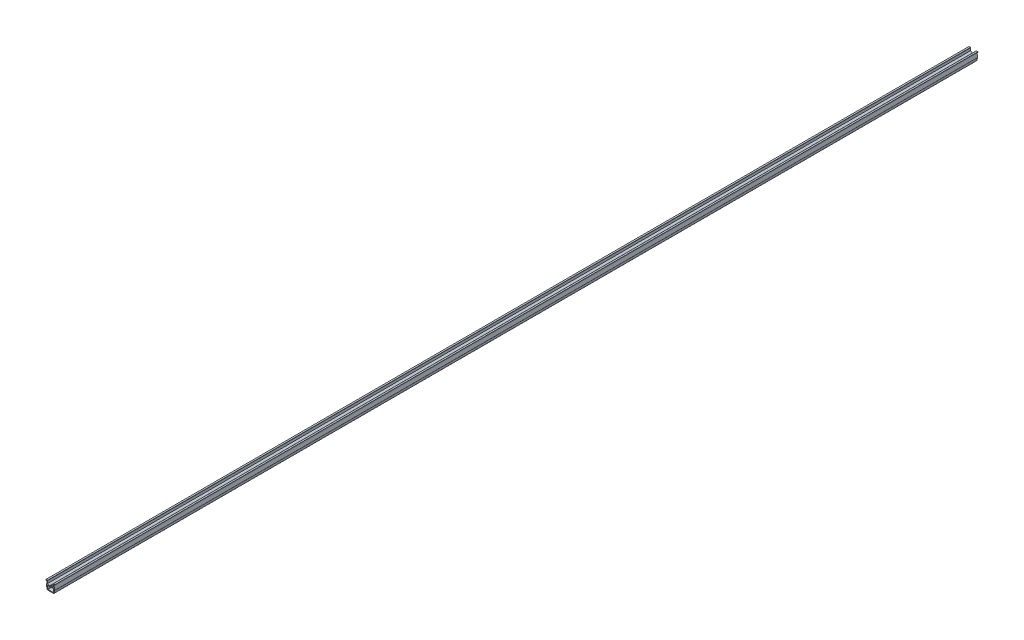
SolidWorks part; units mm, degrees
ref_plane "前视基准面" through (0, 0, 0) normal (0, 0, 1) x (1, 0, 0)
ref_plane "上视基准面" through (0, 0, 0) normal (0, 1, 0) x (1, 0, 0)
ref_plane "右视基准面" through (0, 0, 0) normal (1, 0, 0) x (0, 0, -1)
sketch "草图1" plane through (0, 0, 0) normal (0, 0, 1) x (1, 0, 0)
  line L0 (1.0438, 81.1403) -> (1.0438, 80.3403)
  line L1 (10.8438, 81.1403) -> (10.8438, 80.3403)
  line L2 (9.1456, 78.023) -> (8.9881, 80.9194)
  line L3 (9.4254, 75.3628) -> (9.2372, 77.1522)
  line L4 (10.2444, 75.3242) -> (9.8639, 80.3403)
  line L5 (2.8833, 73.1422) -> (2.4692, 75.2125)
  line L6 (2.238, 72.3411) -> (1.6715, 75.1739)
  line L7 (9.0044, 73.1422) -> (9.4185, 75.2125)
  line L8 (9.6709, 72.3411) -> (10.2374, 75.1739)
  line L9 (4.7438, 76.8673) -> (2.7421, 78.023)
  line L10 (4.3438, 76.1745) -> (2.6505, 77.1522)
  line L11 (7.1438, 76.8673) -> (9.1456, 78.023)
  line L12 (7.5438, 76.1745) -> (9.2372, 77.1522)
  line L13 (2.6505, 77.1522) -> (2.4622, 75.3628)
  line L14 (2.8996, 80.9194) -> (2.7421, 78.023)
  line L15 (2.0449, 80.3403) -> (1.6645, 75.3242)
  line L16 (8.5141, 72.7403) -> (3.3735, 72.7403)
  line L17 (9.1806, 71.9392) -> (2.7283, 71.9392)
  line L18 (9.8639, 80.3403) -> (10.8438, 80.3403)
  line L19 (1.0438, 80.3403) -> (2.0449, 80.3403)
  line L20 (9.187, 81.1403) -> (10.8438, 81.1403)
  line L21 (1.0438, 81.1403) -> (2.7007, 81.1403)
  arc A0 (9.187, 81.1403) -> (8.9881, 80.9194) centre (9.187, 80.9403) ccw
  arc A1 (2.8996, 80.9194) -> (2.7007, 81.1403) centre (2.7007, 80.9403) ccw
  arc A2 (9.4185, 75.2125) -> (9.4254, 75.3628) centre (8.9282, 75.3105) ccw
  arc A3 (10.2374, 75.1739) -> (10.2444, 75.3242) centre (9.7471, 75.2719) ccw
  arc A4 (2.8833, 73.1422) -> (3.3735, 72.7403) centre (3.3735, 73.2403) ccw
  arc A5 (2.238, 72.3411) -> (2.7283, 71.9392) centre (2.7283, 72.4392) ccw
  arc A6 (4.3438, 76.1745) -> (4.9438, 76.5209) centre (4.5438, 76.5209) ccw
  arc A7 (6.9438, 76.5209) -> (7.5438, 76.1745) centre (7.3438, 76.5209) ccw
  arc A8 (2.4622, 75.3628) -> (2.4692, 75.2125) centre (2.9595, 75.3105) ccw
  arc A9 (1.6645, 75.3242) -> (1.6715, 75.1739) centre (2.1618, 75.2719) ccw
  arc A10 (8.5141, 72.7403) -> (9.0044, 73.1422) centre (8.5141, 73.2403) ccw
  arc A11 (9.1806, 71.9392) -> (9.6709, 72.3411) centre (9.1806, 72.4392) ccw
  arc A12 (7.1438, 76.8673) -> (6.9438, 76.5209) centre (7.3438, 76.5209) ccw
  arc A13 (4.9438, 76.5209) -> (4.7438, 76.8673) centre (4.5438, 76.5209) ccw
extrude "拉伸1" add sketch "草图1" along normal blind 1000
